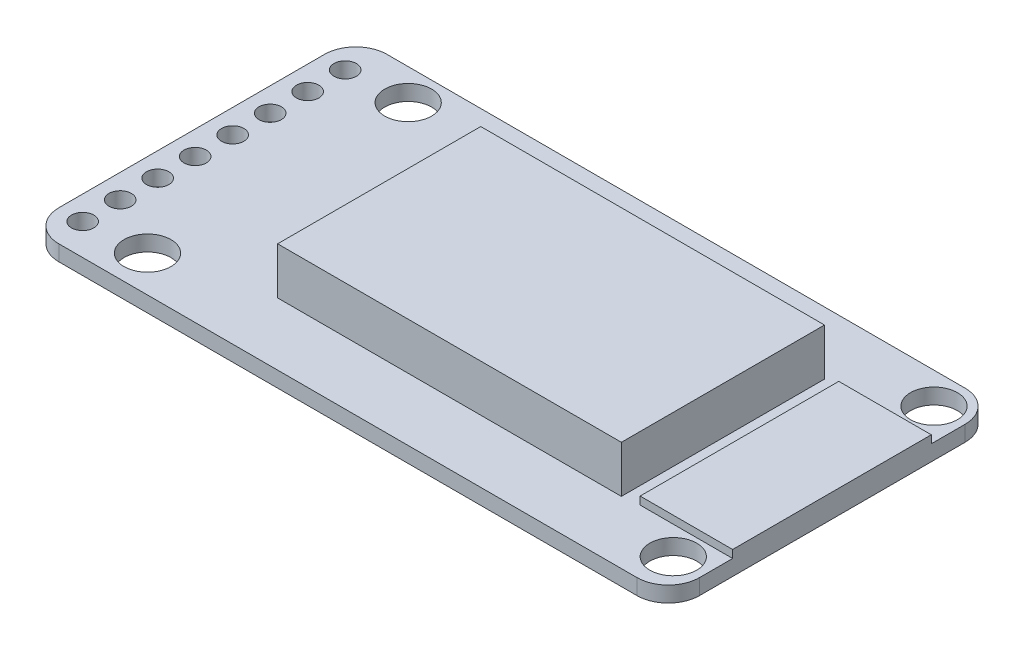
SolidWorks part; units mm, degrees
ref_plane "Alzado" through (0, 0, 0) normal (0, 0, 1) x (1, 0, 0)
ref_plane "Planta" through (0, 0, 0) normal (0, 1, 0) x (1, 0, 0)
ref_plane "Vista lateral" through (0, 0, 0) normal (1, 0, 0) x (0, 0, -1)
sketch "Croquis1" plane through (0, 0, 0) normal (0, 1, 0) x (1, 0, 0)
  line L1 (-20.5, -10.5) -> (20.5, -10.5)
  line L2 (-20.5, -10.5) -> (-20.5, 10.5)
  line L3 (-20.5, 10.5) -> (20.5, 10.5)
  line L4 (20.5, -10.5) -> (20.5, 10.5)
  line L5 (-20.5, -10.5) -> (20.5, 10.5) construction
  line L6 (-20.5, 10.5) -> (20.5, -10.5) construction
  point P0 (0, 0)
  dimension "D1" = 41
  dimension "D2" = 21
extrude "Saliente-Extruir1" add sketch "Croquis1" along normal blind 4
sketch "Croquis2" plane through (0, 4, 0) normal (0, 1, 0) x (1, 0, 0)
  line L0 (-20.5, 10.5) -> (-20.5, 21.8727) construction
  line L1 (-8.5, 21.8727) -> (-8.5, -18.3162) construction
  line L3 (-20.5, 10.5) -> (-8.5, 10.5)
  line L4 (-20.5, 10.5) -> (-20.5, -10.5629)
  line L5 (-20.5, -10.5629) -> (-8.5, -10.5629)
  line L6 (-8.5, 10.5) -> (-8.5, -10.5629)
  dimension "D1" = 12
extrude "Cortar-Extruir1" cut sketch "Croquis2" against normal blind 3
sketch "Croquis3" plane through (0, 4, 0) normal (0, 1, 0) x (1, 0, 0)
  line L0 (20.5, 10.5) -> (20.5, 21.1614) construction
  line L1 (13.5, 10.5) -> (13.5, 21.1614) construction
  line L2 (20.5, 10.5) -> (-8.5, 10.5) construction
  line L4 (13.5, 10.5) -> (20.5, 10.5)
  line L5 (13.5, 10.5) -> (13.5, -10.5)
  line L6 (13.5, -10.5) -> (20.5, -10.5)
  line L7 (20.5, 10.5) -> (20.5, -10.5)
  dimension "D1" = 7
extrude "Cortar-Extruir2" cut sketch "Croquis3" against normal blind 3
sketch "Croquis4" plane through (0, 4, 0) normal (0, 1, 0) x (1, 0, 0)
  line L0 (-7.6331, 6.5) -> (11.8965, 6.5) construction
  line L1 (-6.6738, -6.5) -> (10.389, -6.5) construction
  line L4 (-8.5, -10.5) -> (-8.5, 10.5) construction
  line L5 (-8.5, 6.5) -> (13.5, 6.5)
  line L6 (-8.5, 6.5) -> (-8.5, -6.5)
  line L7 (-8.5, -6.5) -> (13.5, -6.5)
  line L8 (13.5, 6.5) -> (13.5, -6.5)
  line L9 (13.5, 10.5) -> (13.5, -10.5) construction
extrude "Cortar-Extruir3" cut sketch "Croquis4" against normal blind 3 flip side to cut
fillet "Redondeo1" radius 2 4 edges at (-20.5, 0.5, 10.5) (-20.5, 0.5, -10.5) (20.5, 0.5, 10.5) (20.5, 0.5, -10.5)
sketch "Croquis5" plane through (0, 1, 0) normal (0, 1, 0) x (1, 0, 0)
  line L0 (-18.9758, 9.0744) -> (-18.9758, -9.3579) construction
  circle A0 centre (-18.9758, -8.5) radius 0.7153
extrude "Cortar-Extruir5" cut sketch "Croquis5" against normal blind 3 contours A0
pattern_linear "MatrizL2" count 8 spacing 2.4 along (0, 0, -1) of "Cortar-Extruir5"
sketch "Croquis6" plane through (0, 1, 0) normal (0, 1, 0) x (1, 0, 0)
  line L0 (-15.15, 10.5) -> (-15.15, -10.1931) construction
  line L1 (18.5, 10.5) -> (-18.5, 10.5) construction
  line L2 (18.5, 10.5) -> (18.5, -10.5) construction
  line L3 (18.5, 8.5065) -> (-15.15, 8.5065) construction
  line L4 (18.5, -8.1782) -> (-15.15, -8.1782) construction
  circle A0 centre (-15.15, 8.5065) radius 1.5
  circle A1 centre (18.5, 8.5065) radius 1.5
  circle A2 centre (-15.15, -8.1782) radius 1.5
  circle A3 centre (18.5, -8.1782) radius 1.5
extrude "Cortar-Extruir6" cut sketch "Croquis6" against normal blind 3
sketch "Croquis7" plane through (0, 1, 0) normal (0, 1, 0) x (1, 0, 0)
  line L0 (20.5, -8.5) -> (20.5, 8.5) construction
  line L1 (20.5, 6.3331) -> (14.5804, 6.3331)
  line L2 (20.5, 6.3331) -> (20.5, -6.3804)
  line L3 (20.5, -6.3804) -> (14.5804, -6.3804)
  line L4 (14.5804, 6.3331) -> (14.5804, -6.3804)
extrude "Saliente-Extruir2" add sketch "Croquis7" along normal blind 0.5
